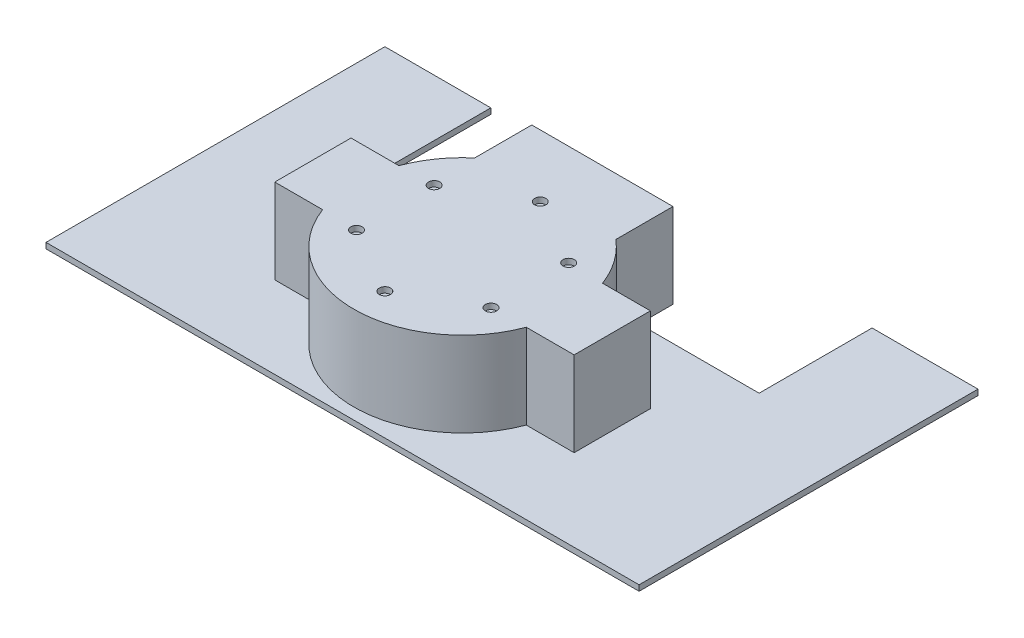
SolidWorks part; units mm, degrees
ref_plane "Front Plane" through (0, 0, 0) normal (0, 0, 1) x (1, 0, 0)
ref_plane "Top Plane" through (0, 0, 0) normal (0, 1, 0) x (1, 0, 0)
ref_plane "Right Plane" through (0, 0, 0) normal (1, 0, 0) x (0, 0, -1)
sketch "Sketch1" plane through (0, 0, 0) normal (0, 1, 0) x (1, 0, 0)
  line L1 (-53, 13.5) -> (53, 13.5)
  line L2 (-53, 13.5) -> (-53, -13.5)
  line L3 (-53, -13.5) -> (53, -13.5)
  line L4 (53, 13.5) -> (53, -13.5)
  line L5 (-25, 49.5) -> (25, 49.5)
  line L6 (-25, 49.5) -> (-25, 27.5)
  line L7 (-25, 27.5) -> (25, 27.5)
  line L8 (25, 49.5) -> (25, 27.5)
  circle A0 centre (0, 0) radius 38.5
  dimension "D5" = 77
  dimension "D1" = 27
  dimension "D2" = 106
  dimension "D3" = 53
  dimension "D4" = 13.5
  dimension "D6" = 49.5
  dimension "D7" = 50
  dimension "D8" = 25
  dimension "D9" = 22
extrude "Boss-Extrude1" add sketch "Sketch1" along normal blind 30 contours L3 A0 | L3 A0 L1 | A0 L1 L2 L3 | L8 A0 L6 L7 | A0 L3 L4 L1 | L1 A0 L8 L7 L6 | A0 L8 L5 L6
sketch "Sketch2" plane through (0, 0, 0) normal (0, -1, 0) x (-1, 0, 0)
  line L1 (105, -42.5) -> (-105, -42.5)
  line L2 (105, -42.5) -> (105, 77.5)
  line L3 (105, 77.5) -> (-105, 77.5)
  line L4 (-105, -42.5) -> (-105, 77.5)
  line L5 (67.5, 37.5) -> (-67.5, 37.5)
  line L6 (67.5, 37.5) -> (67.5, 77.5)
  line L7 (67.5, 77.5) -> (-67.5, 77.5)
  line L8 (-67.5, 37.5) -> (-67.5, 77.5)
  arc M2 (-25, 29.2788) -> (-36.0555, 13.5) centre (0, 0) ccw
  line M3 (-36.0555, 13.5) -> (-53, 13.5)
  line M4 (-53, 13.5) -> (-53, -13.5)
  line M5 (-53, -13.5) -> (-36.0555, -13.5)
  arc M6 (-36.0555, -13.5) -> (36.0555, -13.5) centre (0, 0) ccw
  line M7 (36.0555, -13.5) -> (53, -13.5)
  line M8 (53, -13.5) -> (53, 13.5)
  line M9 (53, 13.5) -> (36.0555, 13.5)
  arc M10 (36.0555, 13.5) -> (25, 29.2788) centre (0, 0) ccw
  line M11 (25, 29.2788) -> (25, 49.5)
  line M13 (-25, 49.5) -> (-25, 29.2788)
  dimension "D5" = 135
  dimension "D1" = 210
  dimension "D2" = 105
  dimension "D3" = 120
  dimension "D4" = 42.5
  dimension "D6" = 37.5
  dimension "D7" = 40
extrude "Boss-Extrude2" add sketch "Sketch2" along normal blind 2 separate body contours L5 L8 L3 L4 L1 L2 L6 M11 M10 M9 M8 M7 M6 M5 M4 M3 M2 M13
sketch "Sketch3" plane through (0, 30, 0) normal (0, 1, 0) x (1, 0, 0)
  circle A0 centre (0, 27.5) radius 2
  circle A1 centre (23.8157, 13.75) radius 2
  circle A2 centre (23.8157, -13.75) radius 2
  circle A3 centre (0, -27.5) radius 2
  circle A4 centre (-23.8157, -13.75) radius 2
  circle A5 centre (-23.8157, 13.75) radius 2
  point P15 (0, 0)
  dimension "D3" = 4
  dimension "D1" = 27.5
  dimension "D2" = 0
  dimension "D4" = 6
extrude "Cut-Extrude1" cut sketch "Sketch3" against normal blind 2
